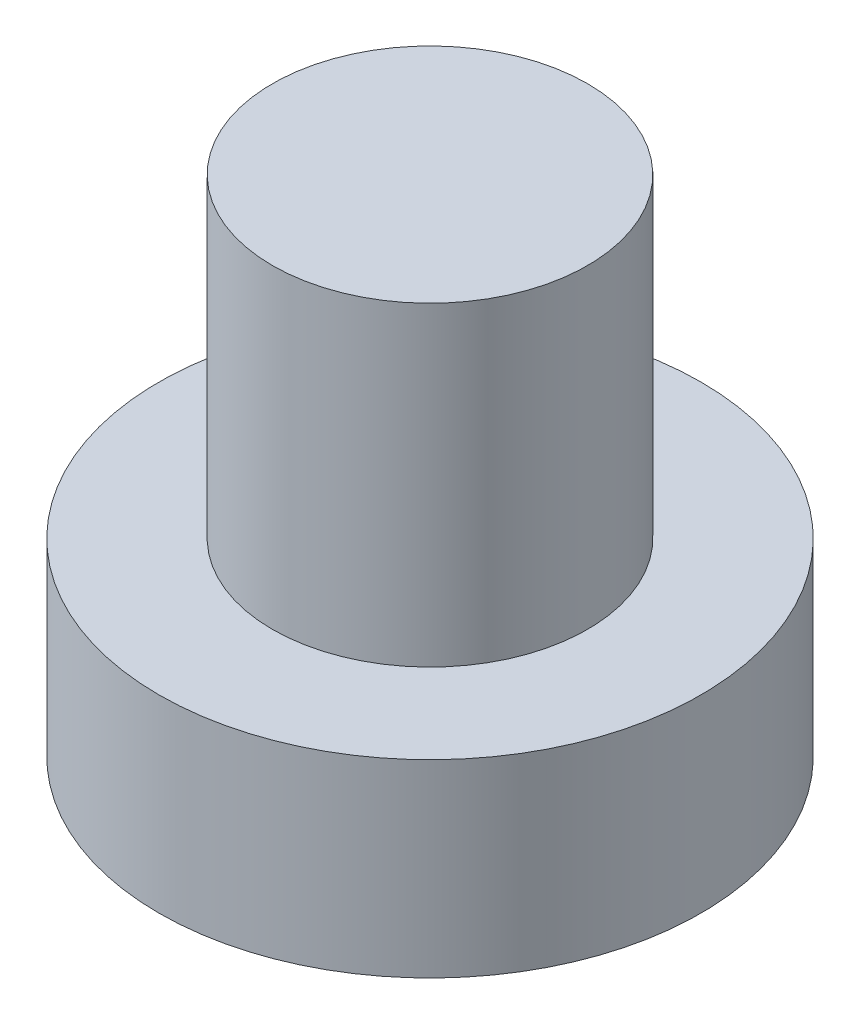
SolidWorks part; units mm, degrees
ref_plane "前视基准面" through (0, 0, 0) normal (0, 0, 1) x (1, 0, 0)
ref_plane "上视基准面" through (0, 0, 0) normal (0, 1, 0) x (1, 0, 0)
ref_plane "右视基准面" through (0, 0, 0) normal (1, 0, 0) x (0, 0, -1)
sketch "草图1" plane through (0, 0, 0) normal (0, 1, 0) x (1, 0, 0)
  circle A0 centre (0, 0) radius 4.3
extrude "凸台-拉伸1" add sketch "草图1" along normal blind 3
sketch "草图2" plane through (0, 3, 0) normal (0, 1, 0) x (1, 0, 0)
  circle A0 centre (0, 0) radius 2.5
extrude "凸台-拉伸2" add sketch "草图2" along normal blind 5
sketch "草图3" plane through (0, 0, 0) normal (0, -1, 0) x (1, 0, 0)
  line L0 (-0.6, 1.1) -> (-0.6, 2.4)
  line L1 (-2.4, -0.6) -> (-1.1, -0.6)
  line L2 (-2.4, -0.6) -> (-2.4, 0.6)
  line L3 (-2.4, 0.6) -> (-1.1, 0.6)
  line L4 (2.4, -0.6) -> (2.4, 0.6)
  line L5 (-2.4, -0.6) -> (2.4, 0.6) construction
  line L6 (-2.4, 0.6) -> (2.4, -0.6) construction
  line L7 (-0.6, -2.4) -> (0.6, -2.4)
  line L8 (-0.6, -2.4) -> (-0.6, -1.1)
  line L9 (-0.6, 2.4) -> (0.6, 2.4)
  line L10 (0.6, -2.4) -> (0.6, -1.1)
  line L11 (-0.6, -2.4) -> (0.6, 2.4) construction
  line L12 (-0.6, 2.4) -> (0.6, -2.4) construction
  line L13 (1.1, -0.6) -> (2.4, -0.6)
  line L14 (0.6, 1.1) -> (0.6, 2.4)
  line L15 (1.1, 0.6) -> (2.4, 0.6)
  arc A0 (-0.6, -1.1) -> (-1.1, -0.6) centre (-1.1, -1.1) ccw
  arc A1 (1.1, -0.6) -> (0.6, -1.1) centre (1.1, -1.1) ccw
  arc A2 (0.6, 1.1) -> (1.1, 0.6) centre (1.1, 1.1) ccw
  arc A3 (-0.6, 1.1) -> (-1.1, 0.6) centre (-1.1, 1.1) cw
  point P0 (0, 0)
  point P6 (0, 0)
  point P21 (0.6, 0.6)
  dimension "D1" = 0.5
extrude "切除-拉伸1" cut sketch "草图3" against normal blind 1.5
